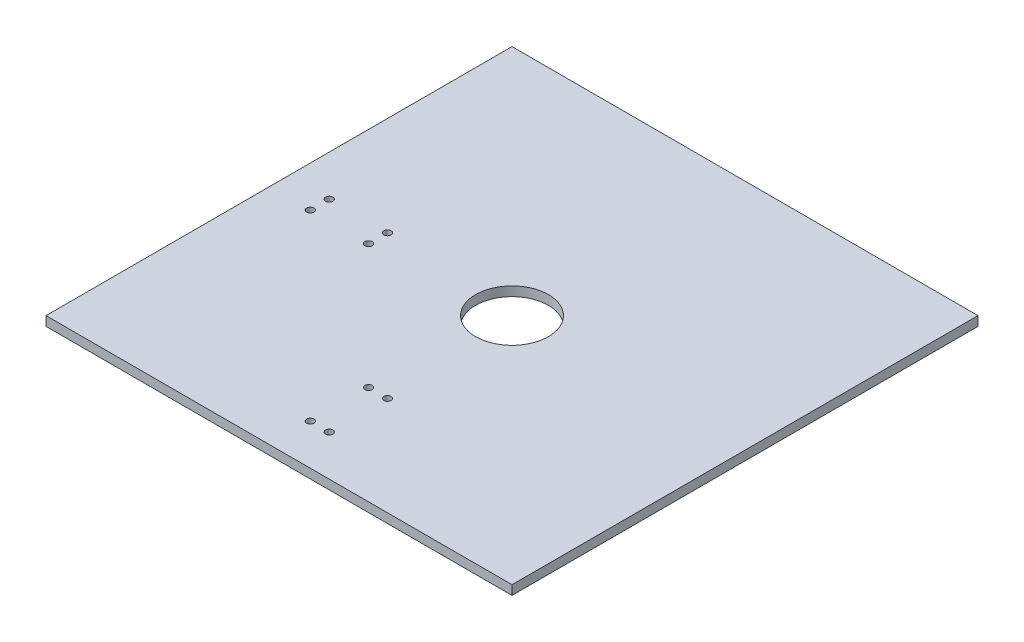
SolidWorks part; units mm, degrees
material "7075-T6, Plate (SS)"
ref_plane "Front Plane" through (0, 0, 0) normal (0, 0, 1) x (1, 0, 0)
ref_plane "Top Plane" through (0, 0, 0) normal (0, 1, 0) x (1, 0, 0)
ref_plane "Right Plane" through (0, 0, 0) normal (1, 0, 0) x (0, 0, -1)
sketch "Sketch1" plane through (0, 0, 0) normal (0, 1, 0) x (1, 0, 0)
  line L1 (-101.6, -101.6) -> (101.6, -101.6)
  line L2 (-101.6, -101.6) -> (-101.6, 101.6)
  line L3 (-101.6, 101.6) -> (101.6, 101.6)
  line L4 (101.6, -101.6) -> (101.6, 101.6)
  line L5 (-101.6, -101.6) -> (101.6, 101.6) construction
  line L6 (-101.6, 101.6) -> (101.6, -101.6) construction
  point P0 (0, 0)
  dimension "D1" = 203.2
  dimension "D2" = 203.2
extrude "Boss-Extrude1" add sketch "Sketch1" along normal blind 4.064
hole_wizard "1/8 (0.125) Diameter Hole1" positions "Sketch2" profile "Sketch3" hole size "1/8" standard "ANSI Inch"
sketch "Sketch2" plane through (0, 4.064, 0) normal (0, 1, 0) x (1, 0, 0)
  line L0 (4.1275, -58.42) -> (-4.1275, -58.42) construction
  line L2 (0, -55) -> (0, 55) construction
  line L3 (-101.6, -101.6) -> (101.6, -101.6) construction
  line L4 (-58.42, -4.1275) -> (-58.42, 4.1275) construction
  line L6 (-55, 0) -> (55, 0) construction
  line L7 (-101.6, 101.6) -> (-101.6, -101.6) construction
  point P0 (-83.82, 4.1275)
  point P2 (-58.42, 4.1275)
  point P4 (-58.42, -4.1275)
  point P6 (-83.82, -4.1275)
  point P8 (-4.1275, -83.82)
  point P10 (-4.1275, -58.42)
  point P12 (4.1275, -58.42)
  point P14 (4.1275, -83.82)
  point P31 (0, -58.42)
  point P40 (-58.42, 0)
  dimension "D1" = 8.255
  dimension "D2" = 17.78
  dimension "D3" = 25.4
  dimension "D4" = 8.255
  dimension "D5" = 17.78
  dimension "D6" = 25.4
sketch "Sketch3" plane through (-83.82, 4.064, -4.1275) normal (1, 0, 0) x (0, 0, 1)
  line L0 (0, 0) -> (0, 26.3539)
  line L1 (0, 26.3539) -> (1.5875, 25.4)
  line L2 (1.5875, 25.4) -> (1.5875, 0)
  line L5 (1.5875, 0) -> (0, 0)
  line L10 (0, 26.3539) -> (-1.5875, 25.4) construction
  line L11 (0, -6.35) -> (0, 107.95) construction
  dimension "Hole Dia." = 3.175
  dimension "Hole Depth" = 25.4
  dimension "Drill Angle" = 118
hole_wizard "5/8 (0.625) Diameter Hole1" positions "Sketch4" profile "Sketch5" hole size "5/8" standard "ANSI Inch"
sketch "Sketch4" plane through (0, 4.064, 0) normal (0, 1, 0) x (1, 0, 0)
  point P0 (0, 0)
sketch "Sketch5" plane through (0, 4.064, 0) normal (1, 0, 0) x (0, 0, 1)
  line L0 (0, 0) -> (0, 34.9387)
  line L1 (0, 34.9387) -> (15.875, 25.4)
  line L2 (15.875, 25.4) -> (15.875, 0)
  line L5 (15.875, 0) -> (0, 0)
  line L10 (0, 34.9387) -> (-15.875, 25.4) construction
  line L11 (0, -6.35) -> (0, 107.95) construction
  dimension "Hole Dia." = 31.75
  dimension "Hole Depth" = 25.4
  dimension "Drill Angle" = 118
